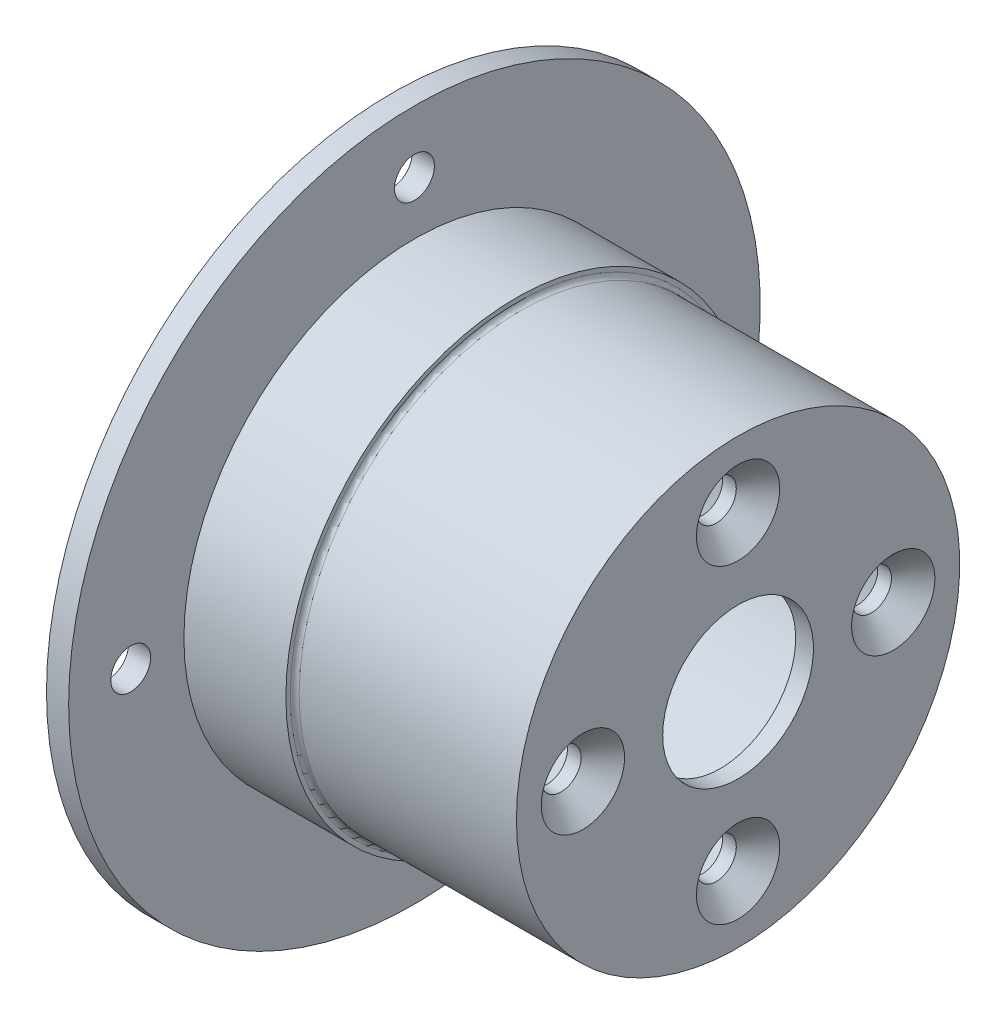
SolidWorks part; units mm, degrees
material "6061 Alloy"
ref_plane "Front Plane" through (0, 0, 0) normal (0, 0, 1) x (1, 0, 0)
ref_plane "Top Plane" through (0, 0, 0) normal (0, 1, 0) x (1, 0, 0)
ref_plane "Right Plane" through (0, 0, 0) normal (1, 0, 0) x (0, 0, -1)
sketch "Sketch2" plane through (0, 0, 0) normal (0, 0, 1) x (1, 0, 0)
  line L0 (-64.1034, 0) -> (113.4236, 0) construction
  line L2 (0, 21) -> (35, 21)
  line L3 (0, -55) -> (0, 55) construction
  line L13 (35, 21) -> (35, 12.5)
  line L14 (35, 12.5) -> (37, 12.5)
  line L21 (0, 26) -> (0, 21)
  line L25 (39, 25) -> (14, 25)
  line L27 (2.5, 26) -> (2.5, 39)
  line L28 (2.5, 39) -> (0, 39)
  line L29 (0, 39) -> (0, 26)
  line L30 (37, 12.5) -> (37, 8.5)
  line L31 (37, 8.5) -> (39, 8.5)
  line L32 (39, 8.5) -> (39, 25)
  line L35 (14, 25) -> (14, 26)
  line L36 (14, 26) -> (2.5, 26)
  point P14 (36, 12.5)
  dimension "D1" = 21
  dimension "D2" = 35
  dimension "D3" = 12.5
  dimension "D4" = 2
  dimension "D5" = 25
  dimension "D6" = 1
  dimension "D7" = 2.5
  dimension "D8" = 39
  dimension "D9" = 11.5
  dimension "D10" = 8.5
  dimension "D11" = 2
revolve "Revolve1" add sketch "Sketch2" angle 360 about L0
hole_wizard "CSK for M4 Flat Head Machine Screw1" positions "Sketch7" profile "Sketch8" countersink size "M4" standard "ANSI Metric" end condition up to next
sketch "Sketch7" plane through (39, 0, 0) normal (1, 0, 0) x (0, 0, -1)
  circle A0 centre (0, 0) radius 17.5
  point P0 (0, 17.5)
  point P2 (17.5, 0)
  point P4 (0, -17.5)
  point P6 (-17.5, 0)
  dimension "D1" = 35
sketch "Sketch8" plane through (39, 17.5, 0) normal (0, 1, 0) x (0, 0, -1)
  line L0 (0, 0) -> (0, 4)
  line L1 (0, 4) -> (2.25, 4)
  line L2 (2.25, 4) -> (2.25, 2.45)
  line L3 (2.25, 2.45) -> (4.7, 0)
  line L5 (4.7, 0) -> (0, 0)
  line L6 (-2.25, 2.45) -> (-4.7, 0) construction
  line L11 (0, -6.35) -> (0, 107.95) construction
  dimension "Thru Hole Dia." = 4.5
  dimension "Thru Hole Depth" = 4
  dimension "Near C'Sink Dia." = 9.4
  dimension "Near C'Sink Angle" = 90
hole_wizard "M4 Clearance Hole1" positions "Sketch5" profile "Sketch6" hole size "M4" standard "ANSI Metric" end condition up to next
sketch "Sketch5" plane through (0, 0, 0) normal (-1, 0, 0) x (0, 0, 1)
  circle A0 centre (0, 0) radius 32
  point P0 (0, 32)
  point P2 (0, -32)
  point P4 (32, 0)
  point P6 (-32, 0)
  dimension "D1" = 64
sketch "Sketch6" plane through (0, 32, 0) normal (0, 1, 0) x (0, 0, 1)
  line L0 (0, 0) -> (0, 2.5)
  line L1 (0, 2.5) -> (2.25, 2.5)
  line L2 (2.25, 2.5) -> (2.25, 0)
  line L5 (2.25, 0) -> (0, 0)
  line L11 (0, -6.35) -> (0, 107.95) construction
  dimension "Thru Hole Dia." = 4.5
  dimension "Thru Hole Depth" = 2.5
fillet "Fillet1" radius 0.5 1 edges at (14, 0, 25)
